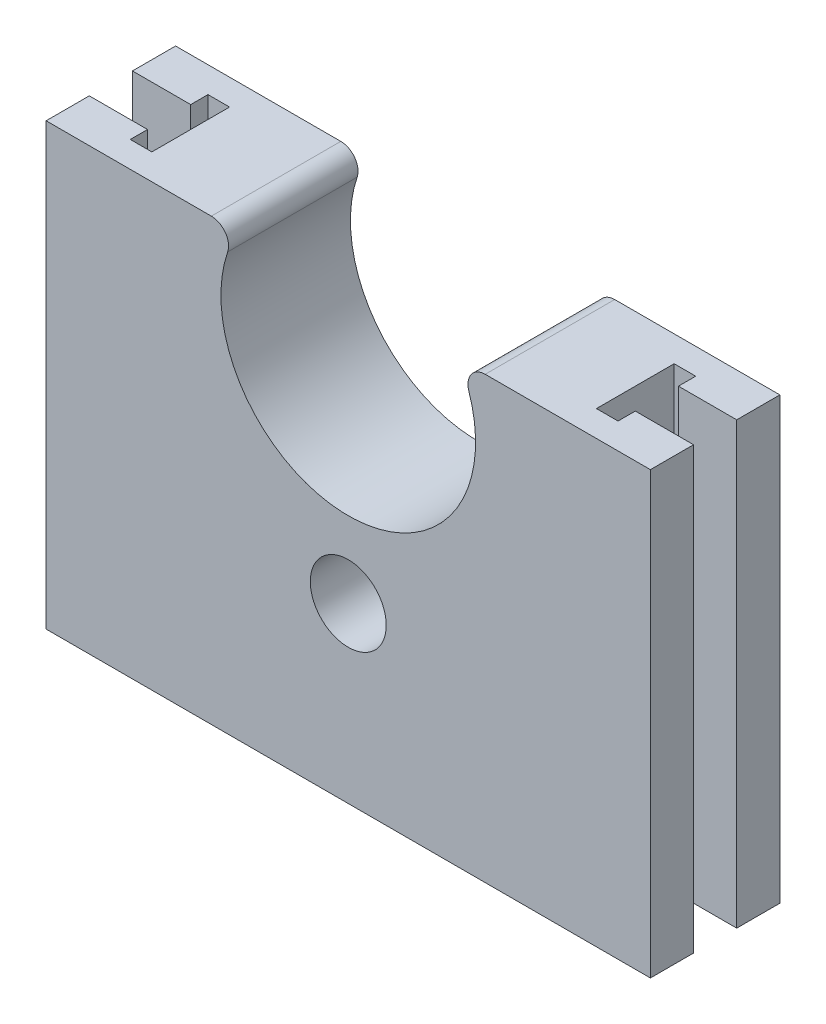
SolidWorks part; units mm, degrees
ref_plane "Front Plane" through (0, 0, 0) normal (0, 0, 1) x (1, 0, 0)
ref_plane "Top Plane" through (0, 0, 0) normal (0, 1, 0) x (1, 0, 0)
ref_plane "Right Plane" through (0, 0, 0) normal (1, 0, 0) x (0, 0, -1)
sketch "Sketch2" plane through (0, 0, 0) normal (0, 0, 1) x (1, 0, 0)
  line L0 (7.4005, 5.8899) -> (7.4005, -22.9851) construction
  line L1 (42.4005, 28.0149) -> (23.2647, 28.0149)
  line L2 (42.4005, 28.0149) -> (42.4005, -22.9851)
  line L3 (42.4005, -22.9851) -> (-27.5995, -22.9851)
  line L4 (-27.5995, 28.0149) -> (-27.5995, -22.9851)
  line L5 (-27.5995, 2.5149) -> (42.4005, 2.5149) construction
  line L6 (-8.4637, 28.0149) -> (-27.5995, 28.0149)
  arc A0 (-6.5694, 25.3731) -> (21.3704, 25.3731) centre (7.4005, 20.6399) ccw
  arc A1 (-8.4637, 28.0149) -> (-6.5694, 25.3731) centre (-8.4637, 26.0149) cw
  arc A2 (23.2647, 28.0149) -> (21.3704, 25.3731) centre (23.2647, 26.0149) ccw
  dimension "D4" = 2
  dimension "D3" = 2
  dimension "D1" = 70
  dimension "D2" = 51
extrude "Boss-Extrude1" add sketch "Sketch2" along normal blind 15
sketch "Sketch3" plane through (0, 28.0149, 0) normal (0, 1, 0) x (1, 0, 0)
  line L0 (-27.5995, -5) -> (-27.5995, 0) construction
  line L5 (42.4005, -15) -> (42.4005, 0) construction
  line L6 (-27.5995, -7.5) -> (42.4005, -7.5) construction
  line L19 (-27.5995, -15) -> (-27.5995, 0) construction
  line L20 (-35.5995, -10) -> (-19.5995, -10)
  line L21 (-35.5995, -10) -> (-35.5995, -5)
  line L22 (-19.5995, -10) -> (-19.5995, -5)
  line L23 (-35.5995, -5) -> (-19.5995, -5)
  line L24 (-35.5995, -10) -> (-19.5995, -5) construction
  line L25 (-19.5995, -10) -> (-35.5995, -5) construction
  line L26 (50.4005, -10) -> (34.4005, -10)
  line L27 (50.4005, -10) -> (50.4005, -5)
  line L28 (34.4005, -10) -> (34.4005, -5)
  line L29 (50.4005, -5) -> (34.4005, -5)
  line L30 (50.4005, -10) -> (34.4005, -5) construction
  line L31 (34.4005, -10) -> (50.4005, -5) construction
  line L32 (-20.8495, -12) -> (-20.8495, -3)
  line L33 (-20.8495, -12) -> (-18.3495, -12)
  line L34 (-20.8495, -3) -> (-18.3495, -3)
  line L35 (-18.3495, -12) -> (-18.3495, -3)
  line L36 (-20.8495, -12) -> (-18.3495, -3) construction
  line L37 (-20.8495, -3) -> (-18.3495, -12) construction
  line L38 (35.6505, -12) -> (33.1505, -12)
  line L39 (35.6505, -12) -> (35.6505, -3)
  line L40 (33.1505, -12) -> (33.1505, -3)
  line L41 (35.6505, -3) -> (33.1505, -3)
  line L42 (35.6505, -12) -> (33.1505, -3) construction
  line L43 (33.1505, -12) -> (35.6505, -3) construction
  line L44 (-27.5995, 0) -> (-20.8495, 0) construction
  line L45 (-8.4637, 0) -> (-27.5995, 0) construction
  line L46 (-20.8495, 0) -> (-18.3495, 0) construction
  line L47 (-20.8495, 0) -> (-20.8495, -3) construction
  point P1 (-19.5995, -7.5)
  point P2 (34.4005, -7.5)
  line M8 (42.4005, -15) -> (42.4005, 0)
  dimension "D2" = 2.5
  dimension "D3" = 9
  dimension "D4" = 9
  dimension "D5" = 2.5
  dimension "D6" = 5
  dimension "D7" = 6.75
  dimension "D8" = 2.5
  dimension "D9" = 16
  dimension "D10" = 5
  dimension "D11" = 5
  dimension "D12" = 16
  dimension "D13" = 3
sketch "Sketch5" plane through (0, 0, 15) normal (0, 0, 1) x (1, 0, 0)
  line L0 (7.4005, 5.8899) -> (7.4005, 1.4899) construction
  line L1 (-27.5995, -22.9851) -> (42.4005, -22.9851) construction
  line L2 (7.4005, 5.8899) -> (7.4005, 1.4899)
  line L3 (7.4005, -7.3101) -> (7.4005, -22.9851) construction
  arc A0 (-6.5694, 25.3731) -> (21.3704, 25.3731) centre (7.4005, 20.6399) ccw construction
  circle A1 centre (7.4005, -2.9101) radius 4.4
  dimension "D2" = 8.8
  dimension "D1" = 8.8
extrude "Cut-Extrude3" cut sketch "Sketch5" against normal through all contours A1
extrude "Cut-Extrude4" cut sketch "Sketch3" against normal through all contours L20 L32 L23 L21 | L39 L26 L29 M8
